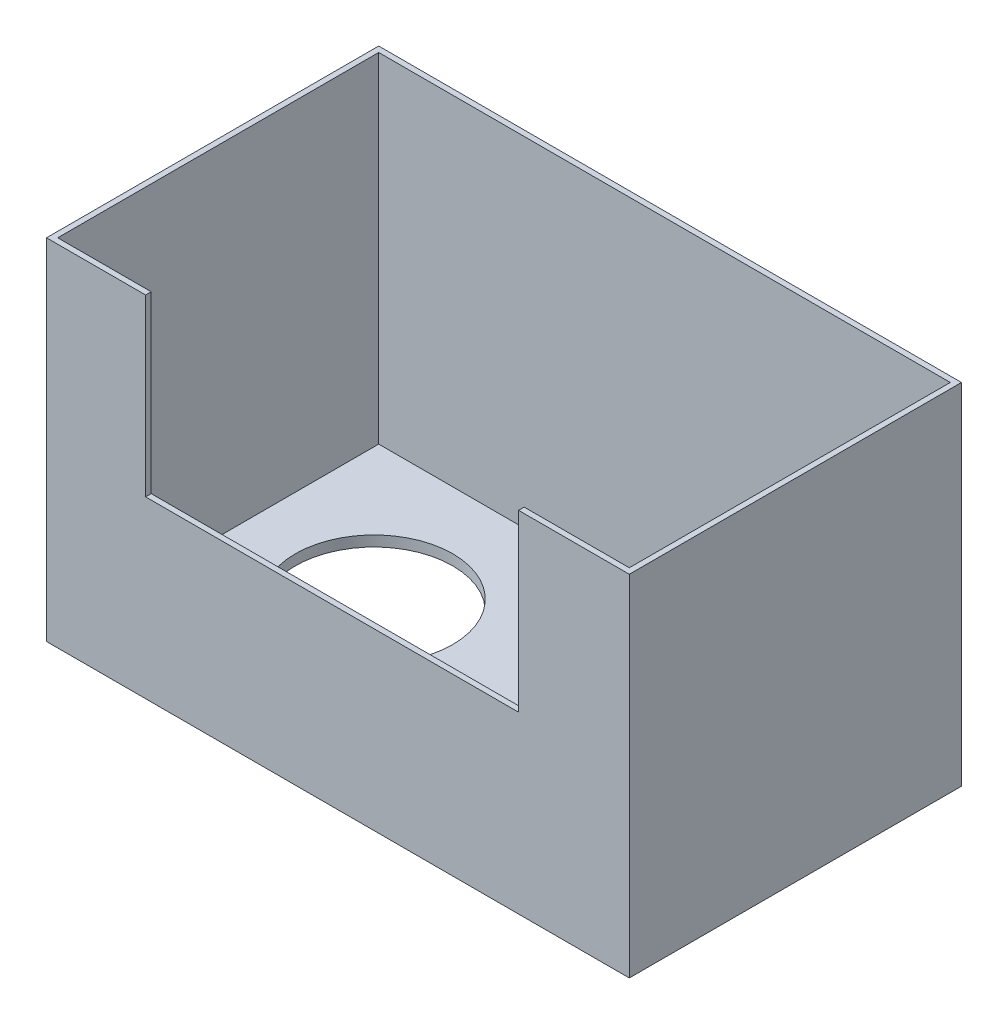
SolidWorks part; units mm, degrees
ref_plane "Front Plane" through (0, 0, 0) normal (0, 0, 1) x (1, 0, 0)
ref_plane "Top Plane" through (0, 0, 0) normal (0, 1, 0) x (1, 0, 0)
ref_plane "Right Plane" through (0, 0, 0) normal (1, 0, 0) x (0, 0, -1)
sketch "Sketch1" plane through (0, 0, 0) normal (0, 1, 0) x (1, 0, 0)
  line L1 (-63.5, 36.195) -> (63.5, 36.195)
  line L2 (-63.5, 36.195) -> (-63.5, -36.195)
  line L3 (-63.5, -36.195) -> (63.5, -36.195)
  line L4 (63.5, 36.195) -> (63.5, -36.195)
  point P4 (0, 36.195)
  point P6 (63.5, 0)
  dimension "D1" = 127
  dimension "D2" = 72.39
extrude "Boss-Extrude1" add sketch "Sketch1" along normal blind 76.2
sketch "Sketch2" plane through (0, 76.2, 0) normal (0, 1, 0) x (1, 0, 0)
  line L0 (-62.2808, 34.9758) -> (-62.2808, -34.9758)
  line L1 (-62.2808, -34.9758) -> (62.2808, -34.9758)
  line L2 (62.2808, -34.9758) -> (62.2808, 34.9758)
  line L3 (62.2808, 34.9758) -> (-62.2808, 34.9758)
  line L4 (-63.5, 36.195) -> (-63.5, -36.195)
  line L5 (-63.5, -36.195) -> (63.5, -36.195)
  line L6 (63.5, -36.195) -> (63.5, 36.195)
  line L7 (63.5, 36.195) -> (-63.5, 36.195)
  line L8 (-63.5, 36.195) -> (-63.5, -36.195) construction
  line L9 (-63.5, -36.195) -> (63.5, -36.195) construction
  line L10 (63.5, -36.195) -> (63.5, 36.195) construction
  line L11 (63.5, 36.195) -> (-63.5, 36.195) construction
  dimension "D1" = 0
  dimension "D2" = 1.2192
extrude "Cut-Extrude1" cut sketch "Sketch2" against normal offset from surface (73.914 mm away) 2.286 up to face at (0, 0, 0)
sketch "Sketch4" plane through (0, 0, 36.195) normal (0, 0, 1) x (1, 0, 0)
  line L0 (-63.5, 76.2) -> (63.5, 76.2) construction
  line L1 (-63.5, 76.2) -> (63.5, 76.2) construction
  line L2 (-63.5, 76.2) -> (-63.5, 0) construction
  line L3 (-41.91, 76.2) -> (39.37, 76.2)
  line L4 (-41.91, 76.2) -> (-41.91, 38.1)
  line L5 (-41.91, 38.1) -> (39.37, 38.1)
  line L6 (39.37, 76.2) -> (39.37, 38.1)
  line L7 (63.5, 76.2) -> (63.5, 0) construction
  dimension "D1" = 21.59
  dimension "D2" = 24.13
  dimension "D3" = 38.1
extrude "Cut-Extrude2" cut sketch "Sketch4" against normal up to surface (1.2192 mm away) up to face at (0, 39.243, 34.9758)
sketch "Sketch5" plane through (0, 0, 0) normal (0, -1, 0) x (1, 0, 0)
  line L0 (-63.5, -36.195) -> (-63.5, 36.195) construction
  line L1 (63.5, -36.195) -> (-63.5, -36.195) construction
  line L2 (0, -36.195) -> (0, 36.195) construction
  line L3 (-63.5, 36.195) -> (63.5, 36.195) construction
  circle A0 centre (-33.528, -5.207) radius 17.145
  circle A2 centre (33.528, -5.207) radius 17.145
  dimension "D3" = 34.29
  dimension "D1" = 29.972
  dimension "D2" = 30.988
extrude "Cut-Extrude3" cut sketch "Sketch5" against normal up to surface (2.286 mm away) up to face at (0, 2.286, 0)
